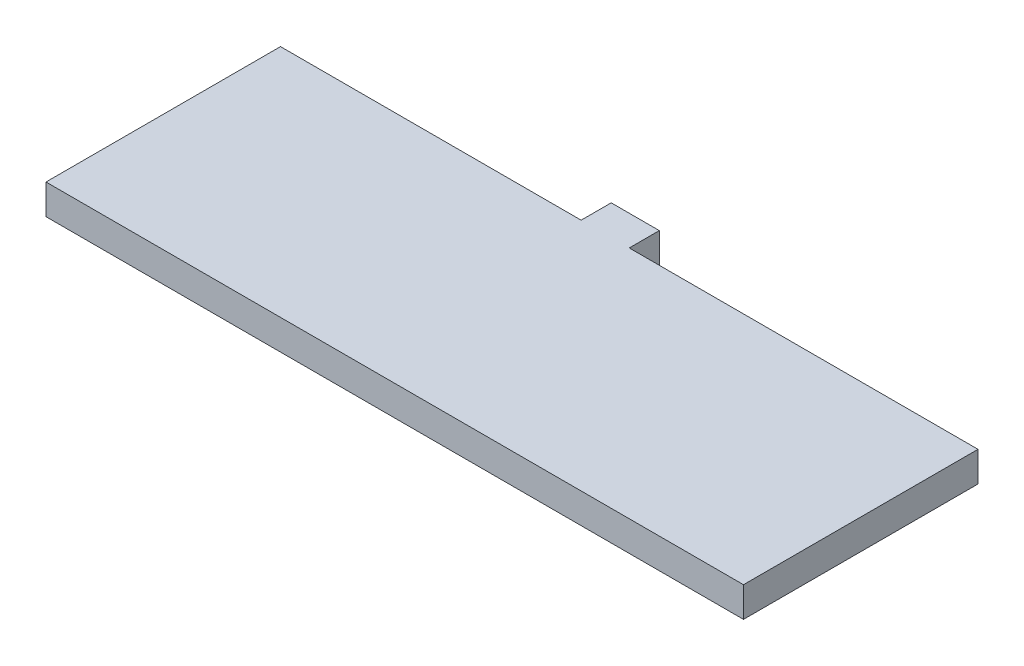
SolidWorks part; units mm, degrees
material "Acrylic (Medium-high impact)"
ref_plane "Front Plane" through (0, 0, 0) normal (0, 0, 1) x (1, 0, 0)
ref_plane "Top Plane" through (0, 0, 0) normal (0, 1, 0) x (1, 0, 0)
ref_plane "Right Plane" through (0, 0, 0) normal (1, 0, 0) x (0, 0, -1)
sketch "Sketch2" plane through (0, 0, 0) normal (0, 1, 0) x (1, 0, 0)
  line L0 (-26.8097, 0) -> (-26.8097, -24.765) construction
  line L1 (-36.83, 0) -> (36.83, 0)
  line L2 (-36.83, 0) -> (-36.83, -24.765)
  line L3 (-36.83, -24.765) -> (36.83, -24.765)
  line L4 (36.83, 0) -> (36.83, -24.765)
  line L5 (-5.08, 0) -> (0, 0)
  line L6 (-5.08, 0) -> (-5.08, 3.175)
  line L7 (-5.08, 3.175) -> (0, 3.175)
  line L8 (0, 0) -> (0, 3.175)
  line L9 (29.9847, 0) -> (29.9847, -24.765) construction
  line L10 (0, 0) -> (0, 3.175) construction
  line L11 (0, 3.175) -> (6.477, 3.175) construction
  line L12 (6.477, 3.175) -> (6.477, 0) construction
  point P8 (0, -24.765)
  point P14 (6.477, 1.5875)
  dimension "D1" = 73.66
  dimension "D2" = 56.7944
  dimension "D3" = 5.08
  dimension "D4" = 27.94
  dimension "D7" = 6.477
  dimension "D8" = 3.175
  dimension "D6" = 23.5077
extrude "Boss-Extrude1" add sketch "Sketch2" along normal blind 3.175 contours L4 L1 L2 L3 | L1 L8 L7 L6
equation "\"bottomThickness\"= .25in"
equation "\"wallThickness\"= .125in"
equation "\"D8@Sketch2\"=\"wallThickness\""
equation "\"D1@Boss-Extrude1\"=\"wallThickness\""
